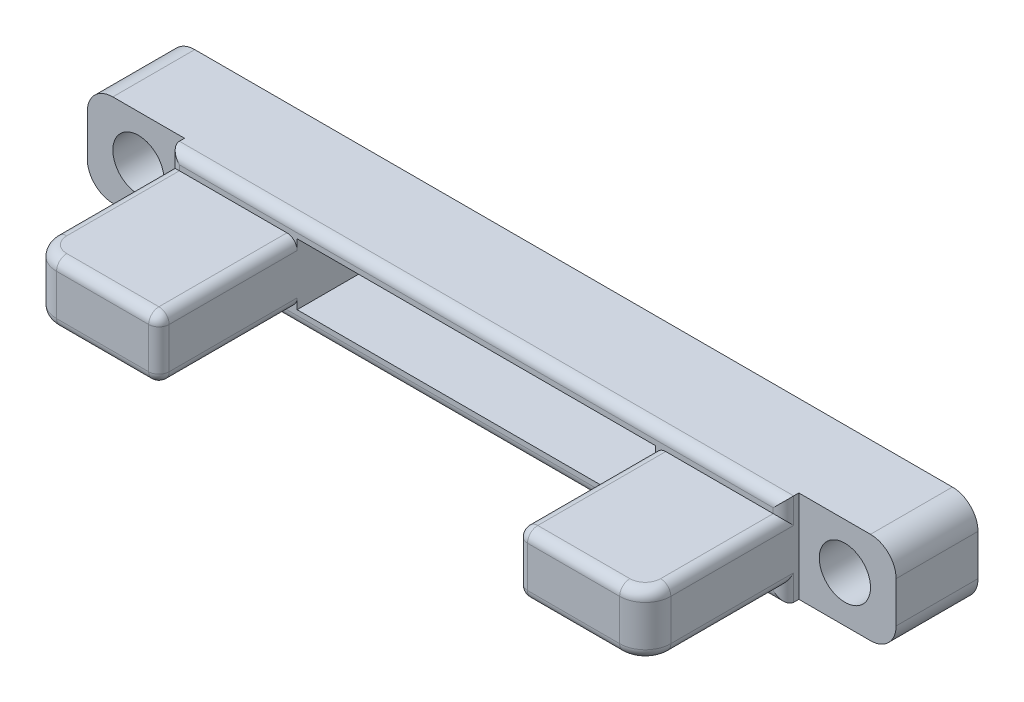
SolidWorks part; units mm, degrees
ref_plane "Front Plane" through (0, 0, 0) normal (0, 0, 1) x (1, 0, 0)
ref_plane "Top Plane" through (0, 0, 0) normal (0, 1, 0) x (1, 0, 0)
ref_plane "Right Plane" through (0, 0, 0) normal (1, 0, 0) x (0, 0, -1)
sketch "Sketch1" plane through (0, 0, 0) normal (0, 0, 1) x (1, 0, 0)
  line L0 (-39.5, 0) -> (39.5, 0) construction
  line L1 (-39.5, 4.5) -> (39.5, 4.5)
  line L2 (-39.5, 4.5) -> (-39.5, -4.5)
  line L3 (-39.5, -4.5) -> (39.5, -4.5)
  line L4 (39.5, 4.5) -> (39.5, -4.5)
  line L5 (-39.5, 4.5) -> (39.5, -4.5) construction
  line L6 (-39.5, -4.5) -> (39.5, 4.5) construction
  line L7 (0, 0) -> (0, 4.5) construction
  circle A1 centre (-34.5, 0) radius 2.5
  circle A2 centre (34.5, 0) radius 2.5
  point P0 (0, 0)
  dimension "D4" = 5
  dimension "D1" = 79
  dimension "D2" = 9
  dimension "D5" = 5
extrude "Boss-Extrude1" add sketch "Sketch1" along normal blind 8
sketch "Sketch2" plane through (0, 0, 8) normal (0, 0, 1) x (1, 0, 0)
  line L0 (0, 4.5) -> (0, -4.5) construction
  line L11 (-39.5, 4.5) -> (39.5, 4.5) construction
  line L12 (-39.5, -4.5) -> (39.5, -4.5) construction
  line L17 (-30, 3) -> (30, 3)
  line L18 (-30, 3) -> (-30, -3)
  line L19 (-30, -3) -> (30, -3)
  line L20 (30, 3) -> (30, -3)
  line L21 (-30, 3) -> (30, -3) construction
  line L22 (-30, -3) -> (30, 3) construction
  point P6 (0, 0)
  dimension "D1" = 60
  dimension "D2" = 6
extrude "Boss-Extrude2" add sketch "Sketch2" along normal blind 15
sketch "Sketch3" plane through (-30, 0, 0) normal (-1, 0, 0) x (0, 0, 1)
  line L0 (8, 0) -> (23, 0) construction
  line L1 (8, 3) -> (8, -3) construction
  line L2 (23, 3) -> (23, -3) construction
  line L3 (8, -4.5) -> (9.5, -4.5)
  line L4 (8, 3) -> (9.5, 3)
  line L5 (8, 3) -> (8, 4.5)
  line L6 (8, 4.5) -> (9.5, 4.5)
  line L7 (9.5, 3) -> (9.5, 4.5)
  line L8 (9.5, -3) -> (9.5, -4.5)
  line L9 (8, -3) -> (9.5, -3)
  line L10 (8, -3) -> (8, -4.5)
extrude "Boss-Extrude3" add sketch "Sketch3" against normal up to surface (60 mm away) up to face at (30, 0, 15.5)
sketch "Sketch4" plane through (0, 0, 23) normal (0, 0, -1) x (-1, 0, 0)
  line L3 (-30, -3) -> (30, -3) construction
  line L6 (17.5, 3) -> (-17.5, 3)
  line L7 (17.5, 3) -> (17.5, -3)
  line L8 (17.5, -3) -> (-17.5, -3)
  line L9 (-17.5, 3) -> (-17.5, -3)
  line L10 (17.5, 3) -> (-17.5, -3) construction
  line L11 (17.5, -3) -> (-17.5, 3) construction
  point P0 (0, 0)
  dimension "D1" = 35
extrude "Cut-Extrude1" cut sketch "Sketch4" along normal up to surface (23 mm away) contours L7 L6 L9 L8 up to face at (0, 0, 0)
fillet "Fillet1" radius 2.5 6 edges at (39.5, -4.5, 4) (39.5, 4.5, 4) (-39.5, -4.5, 4) (-39.5, 4.5, 4) (30, 0, 23) (-30, 0, 23)
fillet "Fillet2" radius 1 24 edges at (0, 4.5, 9.5) (0, -4.5, 9.5) (30, 3, 15) (29.2678, 3, 22.2678) (-22.5, 3, 23) (22.5, 3, 23) (-29.2678, 3, 22.2678) (30, -3, 15) (29.2678, -3, 22.2678) (-22.5, -3, 23) (22.5, -3, 23) (-29.2678, -3, 22.2678) (30, -3.75, 9.5) (-30, -3.75, 9.5) (30, 3.75, 9.5) (-30, 3.75, 9.5) (-30, 3, 15) (-30, -3, 15) (17.5, -3, 16.25) (17.5, 3, 16.25) (17.5, 0, 23) (-17.5, -3, 16.25) (-17.5, 3, 16.25) (-17.5, 0, 23)
